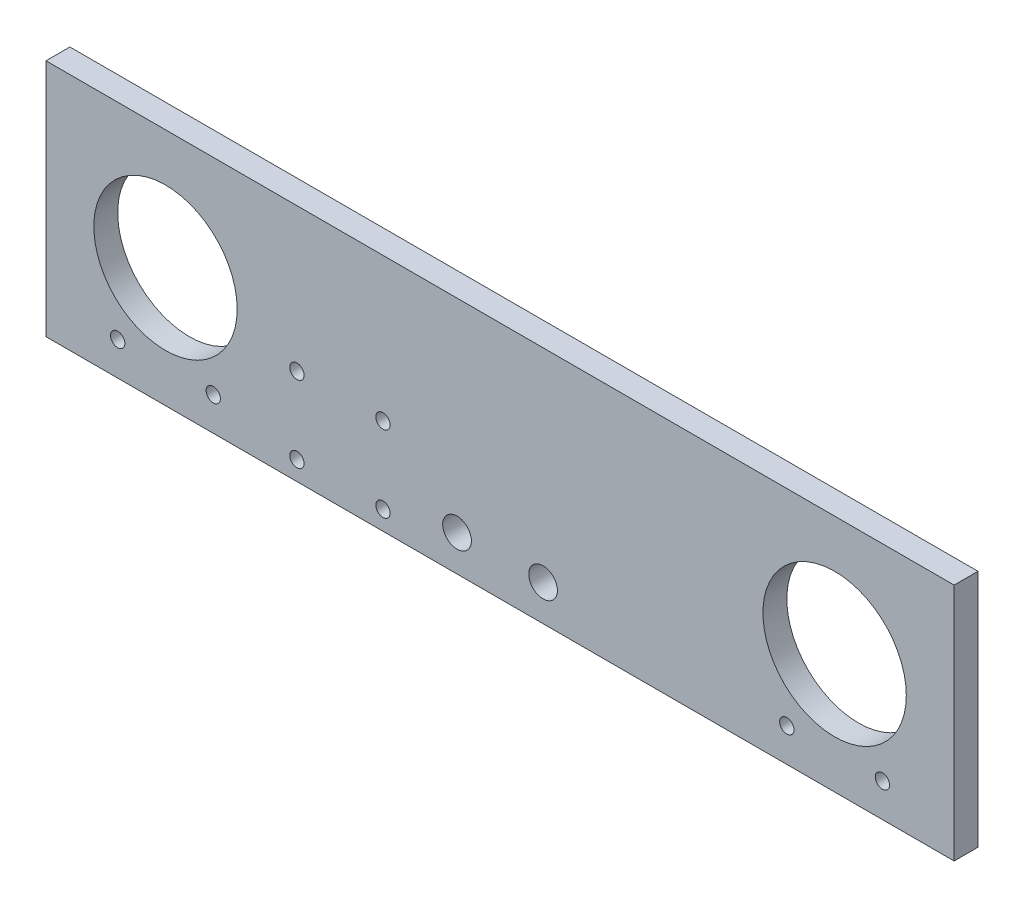
SolidWorks part; units mm, degrees
ref_plane "Front Plane" through (0, 0, 0) normal (0, 0, 1) x (1, 0, 0)
ref_plane "Top Plane" through (0, 0, 0) normal (0, 1, 0) x (1, 0, 0)
ref_plane "Right Plane" through (0, 0, 0) normal (1, 0, 0) x (0, 0, -1)
sketch "Sketch1" plane through (0, 0, 0) normal (0, 0, 1) x (1, 0, 0)
  line L0 (70.5, 21.5) -> (70.5, 18.5) construction
  line L1 (0, 0) -> (190, 0)
  line L2 (0, 0) -> (0, 50)
  line L3 (0, 50) -> (190, 50)
  line L4 (190, 0) -> (190, 50)
  circle A0 centre (25, 25) radius 15
  circle A1 centre (165, 25) radius 15
  circle A2 centre (35, 7) radius 1.5
  circle A3 centre (175, 7) radius 1.5
  circle A4 centre (155, 7) radius 1.5
  circle A5 centre (70.5, 20) radius 1.5
  circle A6 centre (86, 7.5) radius 3
  circle A7 centre (104, 7.5) radius 3
  circle A8 centre (15, 7) radius 1.5
  circle A9 centre (52.5, 4) radius 1.5
  circle A10 centre (52.5, 20) radius 1.5
  circle A11 centre (70.5, 4) radius 1.5
  point P5 (95, 25)
  dimension "D3" = 30
  dimension "D7" = 30
  dimension "D9" = 3
  dimension "D11" = 10
  dimension "D15" = 3
  dimension "D16" = 7
  dimension "D23" = 6
  dimension "D24" = 6
  dimension "D28" = 16
  dimension "D29" = 18
  dimension "D36" = 3
  dimension "D12" = 7
  dimension "D18" = 3
  dimension "D19" = 4
  dimension "D2" = 50
  dimension "D4" = 70
  dimension "D5" = 95
  dimension "D6" = 25
  dimension "D8" = 70
  dimension "D10" = 10
  dimension "D13" = 7
  dimension "D14" = 10
  dimension "D17" = 10
  dimension "D20" = 7
  dimension "D21" = 25
  dimension "D22" = 25
  dimension "D25" = 7.5
  dimension "D26" = 7.5
  dimension "D27" = 9
  dimension "D30" = 27.5
  dimension "D32" = 95
  dimension "D35" = 9
extrude "Boss-Extrude1" add sketch "Sketch1" along normal blind 5
sketch "Sketch2" plane through (0, 0, 5) normal (0, 0, 1) x (1, 0, 0)
  circle A0 centre (15, 7) radius 2.75
  circle A1 centre (35, 7) radius 2.75
  circle A2 centre (155, 7) radius 2.75
  circle A3 centre (175, 7) radius 2.75
  dimension "D1" = 5.5
extrude "Cut-Extrude1" cut sketch "Sketch2" along normal blind 1.5 from surface
